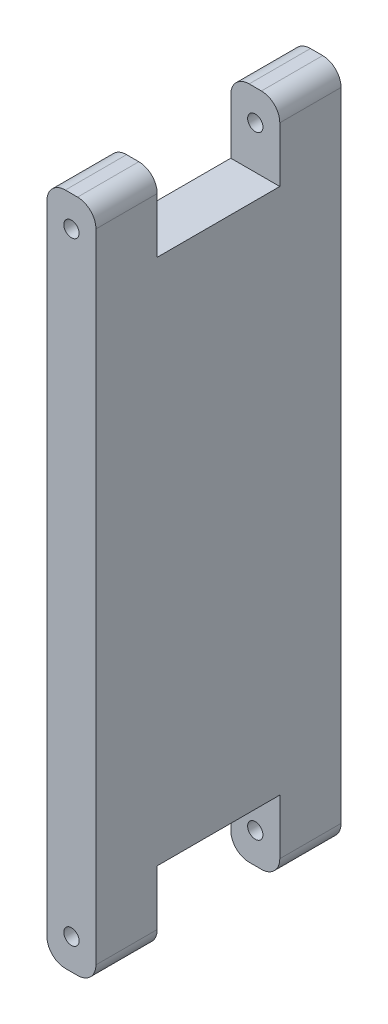
SolidWorks part; units mm, degrees
ref_plane "Front Plane" through (0, 0, 0) normal (0, 0, 1) x (1, 0, 0)
ref_plane "Top Plane" through (0, 0, 0) normal (0, 1, 0) x (1, 0, 0)
ref_plane "Right Plane" through (0, 0, 0) normal (1, 0, 0) x (0, 0, -1)
sketch "Sketch1" plane through (0, 0, 0) normal (0, 0, 1) x (1, 0, 0)
  line L1 (-4, 55) -> (4, 55)
  line L2 (-4, 55) -> (-4, -55)
  line L3 (-4, -55) -> (4, -55)
  line L4 (4, 55) -> (4, -55)
  line L5 (-4, 55) -> (4, -55) construction
  line L6 (-4, -55) -> (4, 55) construction
  point P0 (0, 0)
  dimension "D1" = 8
  dimension "D2" = 110
extrude "Boss-Extrude1" add sketch "Sketch1" against normal blind 40
sketch "Sketch2" plane through (4, 0, 0) normal (1, 0, 0) x (0, 0, -1)
  line L0 (40, 55) -> (0, 55) construction
  line L1 (10, 67) -> (30, 67)
  line L2 (10, 67) -> (10, 43)
  line L3 (10, 43) -> (30, 43)
  line L4 (30, 67) -> (30, 43)
  line L5 (10, 67) -> (30, 43) construction
  line L6 (10, 43) -> (30, 67) construction
  line L7 (0, 0) -> (54.2084, 0) construction
  line L8 (10, -43) -> (30, -67) construction
  line L9 (10, -67) -> (30, -43) construction
  line L10 (30, -67) -> (30, -43)
  line L11 (10, -43) -> (30, -43)
  line L12 (10, -67) -> (10, -43)
  line L13 (10, -67) -> (30, -67)
  line L14 (40, -55) -> (40, 55) construction
  point P0 (20, 55)
  point P14 (20, -55)
  dimension "D1" = 24
  dimension "D2" = 10
extrude "Cut-Extrude1" cut sketch "Sketch2" against normal through all
fillet "Fillet1" radius 3 8 edges at (-4, -55, -35) (4, -55, -35) (-4, -55, -5) (4, -55, -5) (-4, 55, -5) (-4, 55, -35) (4, 55, -35) (4, 55, -5)
sketch "Sketch3" plane through (0, 0, 0) normal (0, 0, 1) x (1, 0, 0)
  line L0 (0, 0) -> (0, 50) construction
  line L1 (1, 55) -> (-1, 55) construction
  line L2 (0, 0) -> (14.6507, 0) construction
  circle A0 centre (0, 50) radius 1.25
  circle A1 centre (0, -50) radius 1.25
  dimension "D1" = 2.5
  dimension "D2" = 5
extrude "Cut-Extrude2" cut sketch "Sketch3" against normal through all
